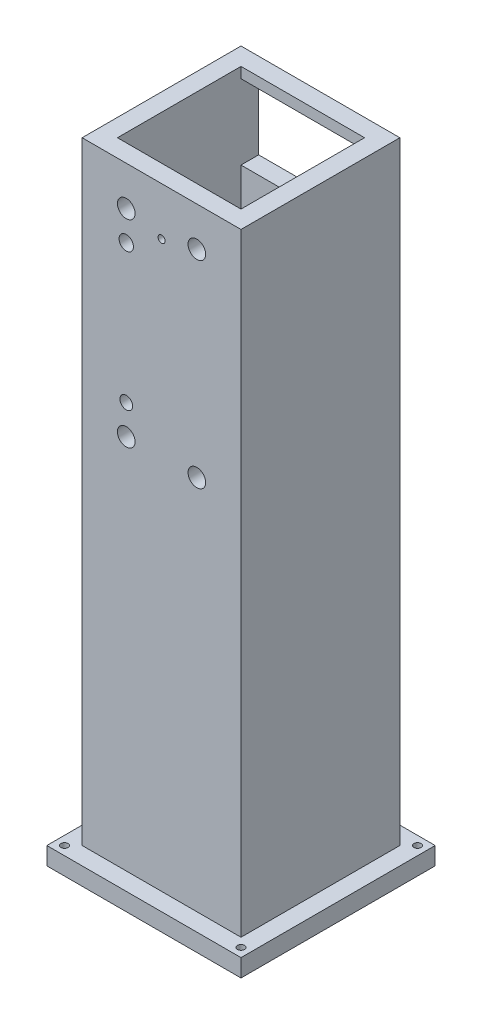
SolidWorks part; units mm, degrees
ref_plane "Alzado" through (0, 0, 0) normal (0, 0, 1) x (1, 0, 0)
ref_plane "Planta" through (0, 0, 0) normal (0, 1, 0) x (1, 0, 0)
ref_plane "Vista lateral" through (0, 0, 0) normal (1, 0, 0) x (0, 0, -1)
sketch "Croquis1" plane through (0, 0, 0) normal (0, 1, 0) x (1, 0, 0)
  line L1 (-22.5, -22.5) -> (22.5, -22.5)
  line L2 (-22.5, -22.5) -> (-22.5, 22.5)
  line L3 (-22.5, 22.5) -> (22.5, 22.5)
  line L4 (22.5, -22.5) -> (22.5, 22.5)
  line L5 (-22.5, -22.5) -> (22.5, 22.5) construction
  line L6 (-22.5, 22.5) -> (22.5, -22.5) construction
  point P0 (0, 0)
  dimension "D1" = 45
  dimension "D2" = 45
extrude "Saliente-Extruir1" add sketch "Croquis1" along normal blind 300
sketch "Croquis4" plane through (-22.5, 0, 0) normal (-1, 0, 0) x (0, 0, 1)
  line L1 (22.5, 300) -> (22.5, 0) construction
  line L3 (55, 0) -> (-55, 0) construction
  line L5 (4.5, 0) -> (4.5, 34)
  line L6 (4.5, 34) -> (22.5, 34)
  line L8 (22.5, 34) -> (22.5, 0)
  line L9 (22.5, 0) -> (4.5, 0)
  dimension "D4" = 34
extrude "Cortar-Extruir2" cut sketch "Croquis4" against normal through all
sketch "Croquis7" plane through (0, 0, 22.5) normal (0, 0, 1) x (1, 0, 0)
  line L0 (0, -24.75) -> (0, 24.75) construction
  line L1 (-22.5, 246.3879) -> (22.5, 246.3879)
  line L2 (-22.5, 246.3879) -> (-22.5, 273.6121)
  line L3 (-22.5, 273.6121) -> (22.5, 273.6121)
  line L4 (22.5, 246.3879) -> (22.5, 273.6121)
  line L5 (-22.5, 246.3879) -> (22.5, 273.6121) construction
  line L6 (-22.5, 273.6121) -> (22.5, 246.3879) construction
  line L7 (22.5, 300) -> (22.5, 34) construction
  point P0 (0, 260)
  dimension "D1" = 260
sketch "Croquis8" plane through (0, 300, 0) normal (0, 1, 0) x (1, 0, 0)
  line L0 (22.5, -22.5) -> (22.5, 22.5) construction
  line L1 (-17.5, -17.5) -> (17.5, -17.5)
  line L2 (-17.5, -17.5) -> (-17.5, 17.5)
  line L3 (-17.5, 17.5) -> (17.5, 17.5)
  line L4 (17.5, -17.5) -> (17.5, 17.5)
  line L5 (-17.5, -17.5) -> (17.5, 17.5) construction
  line L6 (-17.5, 17.5) -> (17.5, -17.5) construction
  line L7 (22.5, 22.5) -> (-22.5, 22.5) construction
  point P0 (0, 0)
  dimension "D1" = 5
  dimension "D2" = 5
extrude "Cortar-Extruir3" cut sketch "Croquis8" against normal through all contours L3 L4 L1 L2
sketch "Croquis9" plane through (0, 0, -22.5) normal (0, 0, -1) x (-1, 0, 0)
  line L0 (22.5, 273.6121) -> (-22.5, 246.3879) construction
  line L1 (-17.5, 249.4128) -> (17.5, 249.4128)
  line L2 (-17.5, 249.4128) -> (-17.5, 270.5872)
  line L3 (-17.5, 270.5872) -> (17.5, 270.5872)
  line L4 (17.5, 249.4128) -> (17.5, 270.5872)
  line L5 (-17.5, 249.4128) -> (17.5, 270.5872) construction
  line L6 (-17.5, 270.5872) -> (17.5, 249.4128) construction
  line L7 (22.5, 246.3879) -> (22.5, 273.6121) construction
  point P0 (0, 260)
  point P10 (22.5, 260)
  dimension "D1" = 5
extrude "Cortar-Extruir4" cut sketch "Croquis9" against normal blind 10 contours L4 L3 L2 L1
sketch "Croquis10" plane through (0, 0, 22.5) normal (0, 0, 1) x (1, 0, 0)
  circle A0 centre (0, 260) radius 1
  dimension "D1" = 2
extrude "Cortar-Extruir5" cut sketch "Croquis10" against normal blind 10
sketch "Croquis11" plane through (0, 0, 22.5) normal (0, 0, 1) x (1, 0, 0)
  line L0 (22.5, 300) -> (22.5, 34) construction
  line L1 (-22.5, 300) -> (22.5, 300)
  line L2 (-22.5, 300) -> (-22.5, 273.6121)
  line L3 (-22.5, 273.6121) -> (22.5, 273.6121)
  line L4 (22.5, 300) -> (22.5, 273.6121)
  line L5 (-22.5, 273.6121) -> (22.5, 273.6121) construction
  dimension "D1" = 0
extrude "Cortar-Extruir6" cut sketch "Croquis11" against normal through all
sketch "Croquis12" plane through (0, 0, 22.5) normal (0, 0, 1) x (1, 0, 0)
  line L0 (-22.5, 267.3717) -> (22.5, 246.3879)
  line L1 (-22.5, 246.3879) -> (-22.5, 273.6121) construction
  line L2 (-22.5, 246.3879) -> (22.5, 246.3879) construction
  dimension "D1" = 25
sketch "Croquis13" plane through (0, 0, 0) normal (1, 0, 0) x (0, 0, -1)
  line L0 (-22.5, 273.6121) -> (-22.5, 34) construction
  line L1 (-22.5, 100) -> (22.5, 100)
  line L2 (-22.5, 100) -> (-22.5, 0)
  line L3 (-22.5, 0) -> (22.5, 0)
  line L4 (22.5, 100) -> (22.5, 0)
  line L5 (24.75, 0) -> (-24.75, 0) construction
  line L6 (22.5, 273.6121) -> (22.5, 0) construction
  dimension "D1" = 100
extrude "Cortar-Extruir7" cut sketch "Croquis13" against normal through all both and the other way through all
sketch "Croquis14" plane through (0, 100, 0) normal (0, -1, 0) x (1, 0, 0)
  line L1 (-27.5, -27.5) -> (27.5, -27.5)
  line L2 (-27.5, -27.5) -> (-27.5, 27.5)
  line L3 (-27.5, 27.5) -> (27.5, 27.5)
  line L4 (27.5, -27.5) -> (27.5, 27.5)
  line L5 (-27.5, -27.5) -> (27.5, 27.5) construction
  line L6 (-27.5, 27.5) -> (27.5, -27.5) construction
  point P0 (0, 0)
  dimension "D1" = 27.5
  dimension "D2" = 27.5
extrude "Saliente-Extruir2" add sketch "Croquis14" along normal blind 5 contours L3 L4 L1 L2
sketch "Croquis16" plane through (0, 95, 0) normal (0, -1, 0) x (1, 0, 0)
  circle A0 centre (25, 25) radius 1
  circle A1 centre (-25, 25) radius 1
  circle A2 centre (-25, -25) radius 1
  circle A3 centre (25, -25) radius 1
  dimension "D1" = 2
  dimension "D2" = 2.5
  dimension "D3" = 2.5
  dimension "D4" = 2.5
  dimension "D5" = 2.5
extrude "Cortar-Extruir8" cut sketch "Croquis16" against normal through all both
sketch "Croquis17" plane through (0, 0, 22.5) normal (0, 0, 1) x (1, 0, 0)
  line L0 (0, -30.25) -> (0, 30.25) construction
  circle A0 centre (-10, 262.5026) radius 2.5
  circle A1 centre (-10, 254.1026) radius 2.03
  circle A2 centre (-10, 214.9026) radius 1.7933
  circle A3 centre (-10, 206.5026) radius 2.5
  circle A4 centre (10, 262.5026) radius 2.5
  circle A5 centre (10, 206.5026) radius 2.5
  point P12 (0, 0)
  point P13 (0, 0)
  point P16 (0, 0)
  point P17 (0, 0)
  dimension "D1" = 5
  dimension "D2" = 4.06
  dimension "D3" = 20
  dimension "D4" = 10
  dimension "D5" = 8.4
  dimension "D6" = 8.4
  dimension "D7" = 56
extrude "Cortar-Extruir9" cut sketch "Croquis17" against normal through all both and the other way through all
